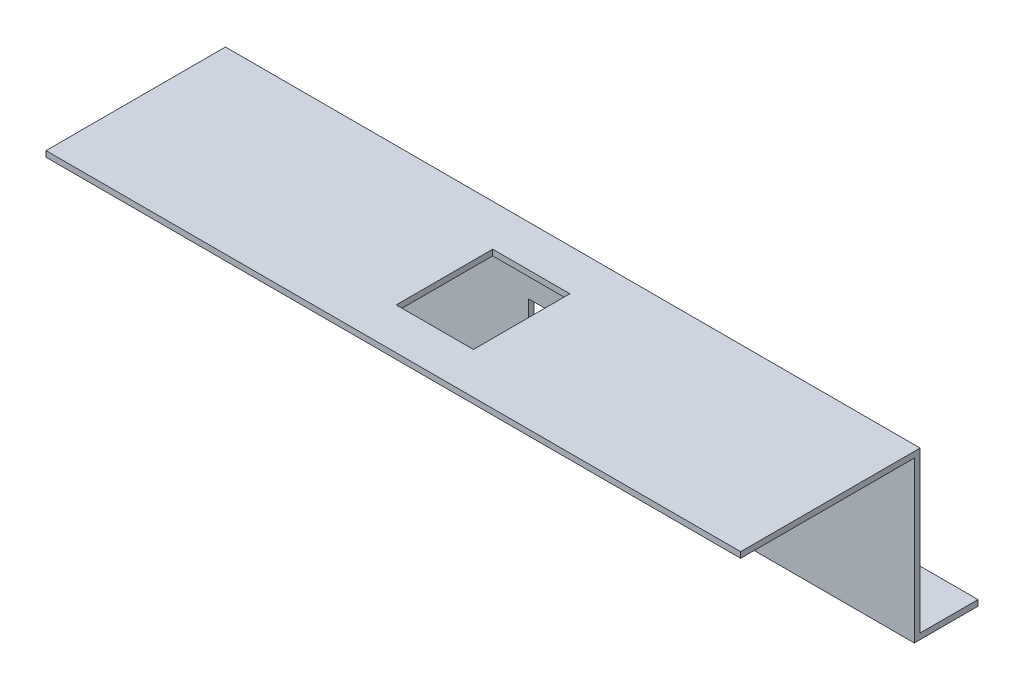
SolidWorks part; units mm, degrees
ref_plane "Front Plane" through (0, 0, 0) normal (0, 0, 1) x (1, 0, 0)
ref_plane "Top Plane" through (0, 0, 0) normal (0, 1, 0) x (1, 0, 0)
ref_plane "Right Plane" through (0, 0, 0) normal (1, 0, 0) x (0, 0, -1)
sketch "Sketch1" plane through (0, 0, 0) normal (1, 0, 0) x (0, 0, -1)
  line L0 (0, 0) -> (0, 45) construction
  line L2 (-0.75, 0) -> (-0.75, 40)
  line L3 (-0.75, 40) -> (-45.75, 40)
  line L4 (-45.75, 40) -> (-45.75, 41.5)
  line L5 (-45.75, 41.5) -> (0.75, 41.5)
  line L6 (0.75, 41.5) -> (0.75, 0)
  line L7 (0.75, 0) -> (15.75, 0)
  line L8 (15.75, 0) -> (15.75, -1.5)
  line L9 (15.75, -1.5) -> (-0.75, -1.5)
  line L10 (-0.75, -1.5) -> (-0.75, 0)
  point P12 (0, 0)
extrude "Boss-Extrude2" add sketch "Sketch1" along normal blind 180
sketch "Sketch2" plane through (0, 0, 0) normal (0, 1, 0) x (1, 0, 0)
  line L0 (90, 0.75) -> (90, 8.25) construction
  line L1 (180, 0.75) -> (0, 0.75) construction
  circle A0 centre (120, 8.25) radius 1.5
  circle A1 centre (90, 8.25) radius 1.5
  circle A2 centre (150, 8.25) radius 1.5
  circle A3 centre (60, 8.25) radius 1.5
  circle A4 centre (30, 8.25) radius 1.5
  dimension "D1" = 3
  dimension "D2" = 3
extrude "Cut-Extrude1" cut sketch "Sketch2" against normal blind 10
sketch "Sketch3" plane through (0, 0, -0.75) normal (0, 0, -1) x (-1, 0, 0)
  line L0 (-90, 41.5) -> (-90, 0) construction
  line L1 (-180, 41.5) -> (0, 41.5) construction
  line L2 (-180, 0) -> (0, 0) construction
  line L4 (-100, 25.75) -> (-80, 25.75)
  line L5 (-100, 25.75) -> (-100, 15.75)
  line L6 (-100, 15.75) -> (-80, 15.75)
  line L7 (-80, 25.75) -> (-80, 15.75)
  line L8 (-100, 25.75) -> (-80, 15.75) construction
  line L9 (-100, 15.75) -> (-80, 25.75) construction
  point P6 (-90, 20.75)
extrude "Cut-Extrude2" cut sketch "Sketch3" against normal blind 10
sketch "Sketch4" plane through (0, 41.5, 0) normal (0, 1, 0) x (1, 0, 0)
  line L0 (90, 0.75) -> (90, -45.75) construction
  line L1 (180, 0.75) -> (0, 0.75) construction
  line L2 (180, -45.75) -> (0, -45.75) construction
  line L4 (80, -10) -> (100, -10)
  line L5 (80, -10) -> (80, -35)
  line L6 (80, -35) -> (100, -35)
  line L7 (100, -10) -> (100, -35)
  line L8 (80, -10) -> (100, -35) construction
  line L9 (80, -35) -> (100, -10) construction
  point P6 (90, -22.5)
extrude "Cut-Extrude3" cut sketch "Sketch4" against normal blind 10
